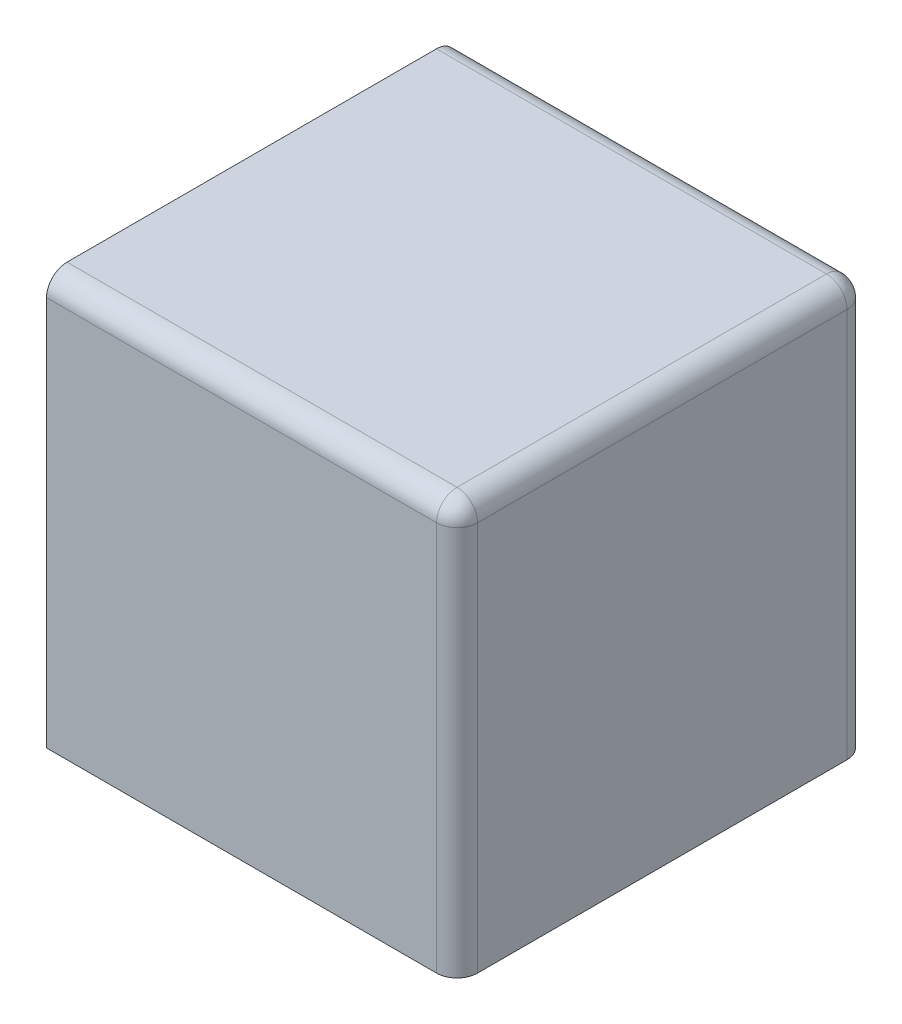
SolidWorks part; units mm, degrees
ref_plane "Front Plane" through (0, 0, 0) normal (0, 0, 1) x (1, 0, 0)
ref_plane "Top Plane" through (0, 0, 0) normal (0, 1, 0) x (1, 0, 0)
ref_plane "Right Plane" through (0, 0, 0) normal (1, 0, 0) x (0, 0, -1)
sketch "Sketch1" plane through (0, 0, 0) normal (0, 1, 0) x (1, 0, 0)
  line L1 (10, 10) -> (-10, 10)
  line L2 (10, 10) -> (10, -10)
  line L3 (10, -10) -> (-10, -10)
  line L4 (-10, 10) -> (-10, -10)
  line L5 (10, 10) -> (-10, -10) construction
  line L6 (10, -10) -> (-10, 10) construction
  point P0 (0, 0)
  dimension "D1" = 20
extrude "Boss-Extrude1" add sketch "Sketch1" along normal blind 20
sketch "Sketch2" plane through (-10, 0, 0) normal (-1, 0, 0) x (0, 0, 1)
  line L0 (-10, 20) -> (10, 20) construction
  circle A0 centre (0, 10) radius 2.5
  dimension "D1" = 5
  dimension "D2" = 10
extrude "Boss-Extrude2" add sketch "Sketch2" along normal blind 6
fillet "Fillet1" radius 1 5 edges at (10, 10, 10) (10, 10, -10) (0, 20, 10) (10, 20, 0) (0, 20, -10)
